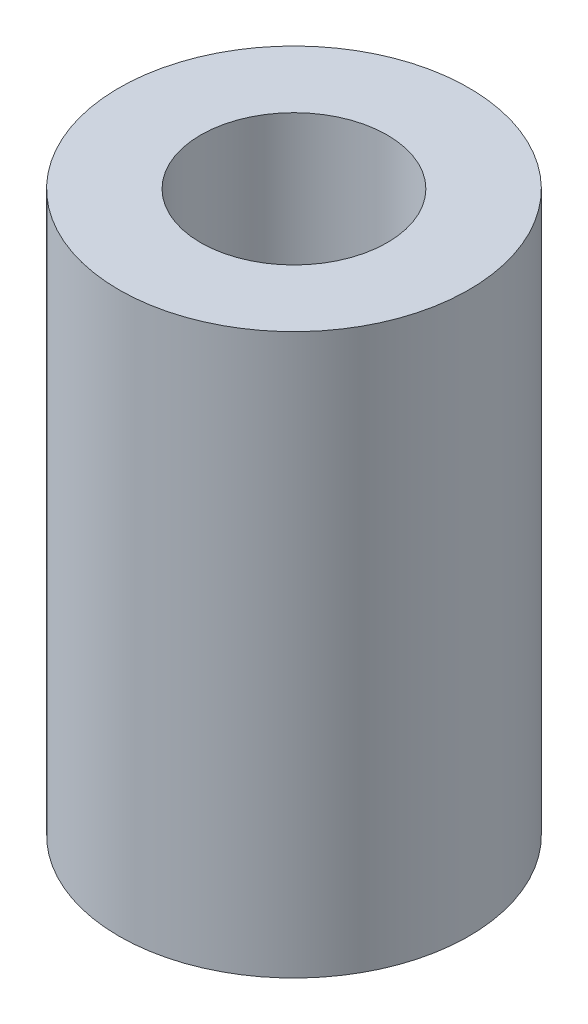
SolidWorks part; units mm, degrees
ref_plane "前视基准面" through (0, 0, 0) normal (0, 0, 1) x (1, 0, 0)
ref_plane "上视基准面" through (0, 0, 0) normal (0, 1, 0) x (1, 0, 0)
ref_plane "右视基准面" through (0, 0, 0) normal (1, 0, 0) x (0, 0, -1)
sketch "草图1" plane through (0, 0, 0) normal (0, 1, 0) x (1, 0, 0)
  circle A0 centre (0, 0) radius 7.5
  dimension "D1" = 15
extrude "凸台-拉伸1" add sketch "草图1" along normal blind 24
sketch "草图2" plane through (0, 24, 0) normal (0, 1, 0) x (1, 0, 0)
  circle A0 centre (0, 0) radius 4
  dimension "D1" = 8
extrude "切除-拉伸1" cut sketch "草图2" against normal through all
